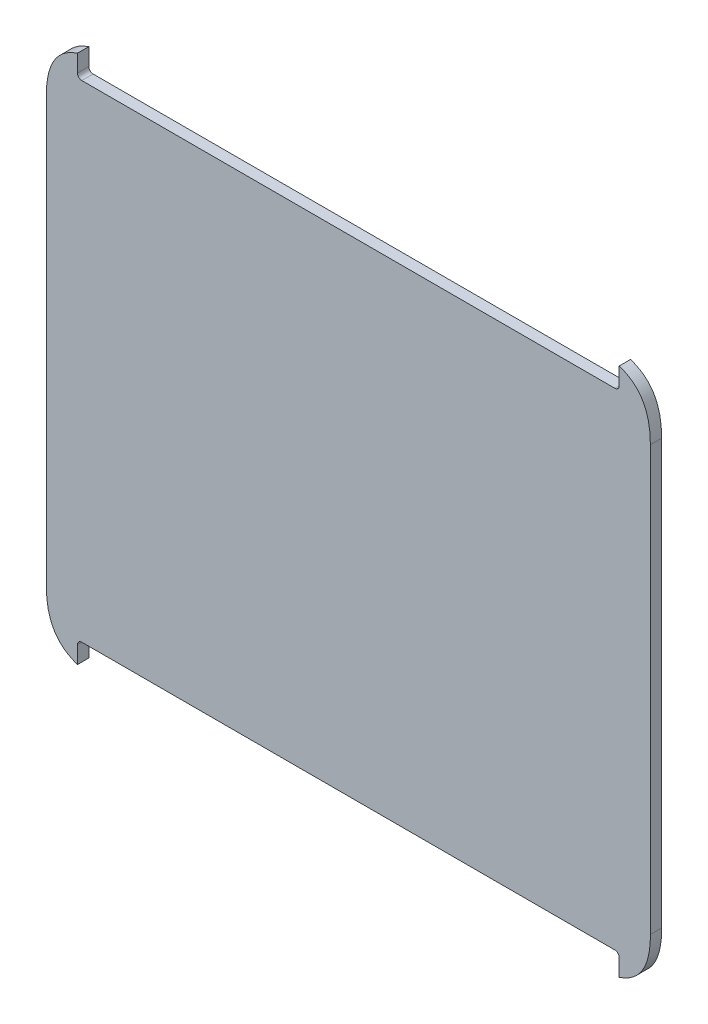
SolidWorks part; units mm, degrees
material "PVC Rigid"
ref_plane "Front Plane" through (0, 0, 0) normal (0, 0, 1) x (1, 0, 0)
ref_plane "Top Plane" through (0, 0, 0) normal (0, 1, 0) x (1, 0, 0)
ref_plane "Right Plane" through (0, 0, 0) normal (1, 0, 0) x (0, 0, -1)
sketch "Sketch1" plane through (0, 0, 0) normal (0, 0, 1) x (1, 0, 0)
  line L1 (-20.574, -61.0845) -> (578.5694, -61.0845)
  line L3 (-20.574, -607.7577) -> (578.5694, -607.7577)
  line L6 (-60.43, -147.1227) -> (-60.43, -131.9766) construction
  line L7 (-25.4, -612.5837) -> (-25.4, -631.9307)
  line L10 (-25.4, -56.2585) -> (-25.4, -36.9114)
  line L11 (-60.43, -96.1144) -> (-60.43, -572.7277)
  line L12 (-60.43, -334.4211) -> (-39.9567, -334.4211) construction
  line L15 (583.3954, -56.2585) -> (583.3954, -36.9114)
  line L16 (618.4254, -96.1144) -> (618.4254, -572.7277)
  line L17 (583.3954, -612.5837) -> (583.3954, -631.9307)
  arc A0 (-25.4, -612.5837) -> (-20.574, -607.7577) centre (-20.574, -612.5837) cw
  arc A1 (-20.574, -61.0845) -> (-25.4, -56.2585) centre (-20.574, -56.2585) cw
  arc A2 (578.5694, -61.0845) -> (583.3954, -56.2585) centre (578.5694, -56.2585) ccw
  arc A3 (583.3954, -612.5837) -> (578.5694, -607.7577) centre (578.5694, -612.5837) ccw
  spline S0 degree 3 poles (-25.4, -36.9114) (-52.8949, -46.0339) (-60.43, -69.6744) (-60.43, -96.1144) knots 0 0 0 0 1 1 1 1
  spline S1 degree 3 poles (-25.4, -631.9307) (-52.8949, -622.8082) (-60.43, -599.1677) (-60.43, -572.7277) knots 0 0 0 0 1 1 1 1
  spline S2 degree 3 poles (583.3954, -36.9114) (610.8903, -46.0339) (618.4254, -69.6744) (618.4254, -96.1144) knots 0 0 0 0 1 1 1 1
  spline S3 degree 3 poles (583.3954, -631.9307) (610.8903, -622.8082) (618.4254, -599.1677) (618.4254, -572.7277) knots 0 0 0 0 1 1 1 1
  point P28 (-25.4, -607.7577)
  point P31 (-25.4, -61.0845)
  dimension "D1" = 4.826
extrude "Boss-Extrude1" add sketch "Sketch1" along normal up to surface (12.7 mm away)
sketch "Sketch2" plane through (0, 0, 12.7) normal (0, 0, 1) x (1, 0, 0)
  line L0 (278.9977, -61.0845) -> (278.9977, -607.7577) construction
  line L1 (-20.574, -61.0845) -> (578.5694, -61.0845) construction
  line L2 (578.5694, -607.7577) -> (-20.574, -607.7577) construction
  line L3 (-60.43, -334.4211) -> (618.4254, -334.4211) construction
  line L4 (-60.43, -572.7277) -> (-60.43, -96.1144) construction
  line L5 (618.4254, -96.1144) -> (618.4254, -572.7277) construction
  line L6 (278.9977, -334.4211) -> (5.6611, -61.0845) construction
  line L8 (259.2757, -260.8175) -> (75.5835, -77.1253)
  line L9 (61.4414, -77.1253) -> (21.702, -116.8647)
  line L10 (21.702, -131.0069) -> (205.3942, -314.699)
  line L11 (21.702, -116.8647) -> (21.702, -131.0069)
  line L12 (75.5835, -77.1253) -> (61.4414, -77.1253)
  line L13 (59.5322, -114.9555) -> (207.1557, -262.579) construction
  line L14 (68.5124, -105.9753) -> (216.1359, -253.5988)
  line L15 (50.5519, -123.9358) -> (198.1754, -271.5593)
  line L16 (482.4119, -77.1253) -> (298.7197, -260.8175)
  line L17 (352.6013, -314.699) -> (536.2935, -131.0069)
  line L18 (536.2935, -131.0069) -> (536.2935, -116.8647)
  line L19 (536.2935, -116.8647) -> (496.5541, -77.1253)
  line L20 (496.5541, -77.1253) -> (482.4119, -77.1253)
  line L21 (536.2935, -537.8353) -> (352.6013, -354.1431)
  line L22 (298.7197, -408.0246) -> (482.4119, -591.7168)
  line L23 (482.4119, -591.7168) -> (496.5541, -591.7168)
  line L24 (496.5541, -591.7168) -> (536.2935, -551.9774)
  line L25 (536.2935, -551.9774) -> (536.2935, -537.8353)
  line L26 (75.5835, -591.7168) -> (259.2757, -408.0246)
  line L27 (205.3942, -354.1431) -> (21.702, -537.8353)
  line L28 (21.702, -537.8353) -> (21.702, -551.9774)
  line L29 (21.702, -551.9774) -> (61.4414, -591.7168)
  line L30 (61.4414, -591.7168) -> (75.5835, -591.7168)
  line L31 (489.483, -105.9753) -> (341.8595, -253.5988)
  line L32 (507.4435, -123.9358) -> (359.82, -271.5593)
  line L33 (498.4632, -114.9555) -> (350.8398, -262.579) construction
  line L34 (507.4435, -544.9063) -> (359.82, -397.2829)
  line L35 (489.483, -562.8668) -> (341.8595, -415.2434)
  line L36 (498.4632, -553.8866) -> (350.8398, -406.2631) construction
  line L37 (68.5124, -562.8668) -> (216.1359, -415.2434)
  line L38 (50.5519, -544.9063) -> (198.1754, -397.2829)
  line L39 (59.5322, -553.8866) -> (207.1557, -406.2631) construction
  circle A0 centre (278.9977, -334.4211) radius 50.8
  arc A1 (205.3942, -314.699) -> (205.3942, -354.1431) centre (278.9977, -334.4211) ccw
  arc A2 (68.5124, -105.9753) -> (50.5519, -123.9358) centre (59.5322, -114.9555) ccw
  arc A3 (198.1754, -271.5593) -> (216.1359, -253.5988) centre (207.1557, -262.579) ccw
  circle A4 centre (278.9977, -334.4211) radius 76.2 construction
  arc A5 (298.7197, -260.8175) -> (259.2757, -260.8175) centre (278.9977, -334.4211) ccw
  arc A6 (352.6013, -354.1431) -> (352.6013, -314.699) centre (278.9977, -334.4211) ccw
  arc A7 (259.2757, -408.0246) -> (298.7197, -408.0246) centre (278.9977, -334.4211) ccw
  arc A8 (507.4435, -123.9358) -> (489.483, -105.9753) centre (498.4632, -114.9555) ccw
  arc A9 (341.8595, -253.5988) -> (359.82, -271.5593) centre (350.8398, -262.579) ccw
  arc A10 (489.483, -562.8668) -> (507.4435, -544.9063) centre (498.4632, -553.8866) ccw
  arc A11 (359.82, -397.2829) -> (341.8595, -415.2434) centre (350.8398, -406.2631) ccw
  arc A12 (50.5519, -544.9063) -> (68.5124, -562.8668) centre (59.5322, -553.8866) ccw
  arc A13 (216.1359, -415.2434) -> (198.1754, -397.2829) centre (207.1557, -406.2631) ccw
  arc A14 (298.7197, -260.8175) -> (259.2757, -260.8175) centre (278.9977, -334.4211) ccw
  arc A15 (298.7197, -260.8175) -> (259.2757, -260.8175) centre (278.9977, -334.4211) ccw
  arc A16 (298.7197, -260.8175) -> (259.2757, -260.8175) centre (278.9977, -334.4211) ccw
  arc A17 (205.3942, -314.699) -> (205.3942, -354.1431) centre (278.9977, -334.4211) ccw
  arc A18 (205.3942, -314.699) -> (205.3942, -354.1431) centre (278.9977, -334.4211) ccw
  arc A19 (205.3942, -314.699) -> (205.3942, -354.1431) centre (278.9977, -334.4211) ccw
  arc A20 (259.2757, -408.0246) -> (298.7197, -408.0246) centre (278.9977, -334.4211) ccw
  arc A21 (259.2757, -408.0246) -> (298.7197, -408.0246) centre (278.9977, -334.4211) ccw
  arc A22 (259.2757, -408.0246) -> (298.7197, -408.0246) centre (278.9977, -334.4211) ccw
  arc A23 (352.6013, -354.1431) -> (352.6013, -314.699) centre (278.9977, -334.4211) ccw
  arc A24 (352.6013, -354.1431) -> (352.6013, -314.699) centre (278.9977, -334.4211) ccw
  arc A25 (352.6013, -354.1431) -> (352.6013, -314.699) centre (278.9977, -334.4211) ccw
  point P20 (68.5124, -70.0543)
  point P21 (14.6309, -123.9358)
  point P23 (133.3439, -188.7673)
  point P53 (278.9977, -334.4211)
  point P56 (424.6515, -188.7673)
  point P63 (424.6515, -480.0748)
  point P70 (133.3439, -480.0748)
  point P75 (278.9977, -334.4211)
  dimension "D1" = 101.6
  dimension "D9" = 12.7
  dimension "D3" = 45
  dimension "D4" = 76.2
  dimension "D5" = 25.4
  dimension "D6" = 12.7
  dimension "D2" = 25.4
  dimension "D10" = 4
  dimension "D11" = 4
